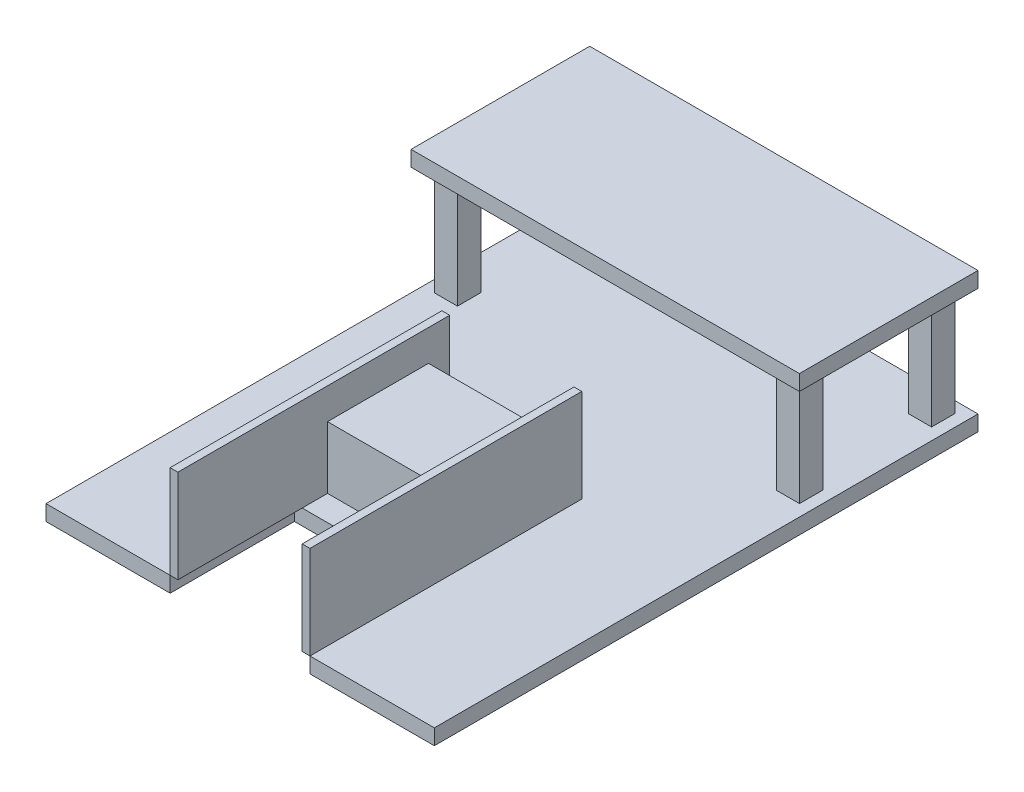
SolidWorks part; units mm, degrees
ref_plane "Front Plane" through (0, 0, 0) normal (0, 0, 1) x (1, 0, 0)
ref_plane "Top Plane" through (0, 0, 0) normal (0, 1, 0) x (1, 0, 0)
ref_plane "Right Plane" through (0, 0, 0) normal (1, 0, 0) x (0, 0, -1)
sketch "Sketch2" plane through (0, 0, 0) normal (0, 1, 0) x (1, 0, 0)
  line L0 (-125, 175) -> (-125, -175)
  line L1 (-125, 175) -> (125, 175)
  line L2 (-125, -175) -> (-45, -175)
  line L3 (125, 175) -> (125, -175)
  line L4 (-125, 175) -> (125, -175) construction
  line L5 (-125, -175) -> (125, 175) construction
  line L6 (0, 192.9969) -> (0, -204.0863) construction
  line L7 (179.2867, 0) -> (-176.6609, 0) construction
  line L8 (-45.0788, -175) -> (-45.0788, -175.07)
  line L9 (-45.0788, -175.07) -> (-45.0788, -95)
  line L10 (-45.0788, -95) -> (44.9212, -95)
  line L11 (44.9652, -175) -> (44.9652, -175.0391)
  line L12 (44.9212, -175) -> (44.9652, -175.0391) construction
  line L13 (-45.0788, -175.07) -> (-45, -175) construction
  line L14 (44.9212, -175) -> (125, -175)
  line L15 (44.9212, -95) -> (44.9212, -175)
  point P1 (0, 0)
  point P11 (0, -135)
  dimension "D1" = 350
  dimension "D2" = 250
  dimension "D3" = 80
  dimension "D4" = 90
  dimension "D5" = 80
  dimension "D6" = 80
extrude "Boss-Extrude1" add sketch "Sketch2" along normal blind 10 contours L10 L15 L14 L3 L1 L0 L2 L9
sketch "Sketch3" plane through (0, 10, 0) normal (0, 1, 0) x (1, 0, 0)
  line L1 (-45.0788, 0) -> (-40.0788, 0)
  line L2 (-45.0788, 0) -> (-45.0788, -175)
  line L3 (-45.0788, -175) -> (-40.0788, -175)
  line L4 (-40.0788, 0) -> (-40.0788, -175)
  line L5 (44.9212, 0) -> (39.9212, 0)
  line L6 (44.9212, 0) -> (44.9212, -175)
  line L7 (44.9212, -175) -> (39.9212, -175)
  line L8 (39.9212, 0) -> (39.9212, -175)
  dimension "D1" = 175
  dimension "D2" = 175
  dimension "D3" = 5
  dimension "D4" = 5
extrude "Boss-Extrude3" add sketch "Sketch3" along normal blind 60 separate body
sketch "Sketch4" plane through (0, 10, 0) normal (0, 1, 0) x (1, 0, 0)
  line L0 (-40.0788, -175) -> (-40.0788, 0) construction
  line L1 (-40.0788, -13.6822) -> (39.9212, -13.6822)
  line L2 (-40.0788, -13.6822) -> (-40.0788, -78.6822)
  line L3 (-40.0788, -78.6822) -> (39.9212, -78.6822)
  line L4 (39.9212, -13.6822) -> (39.9212, -78.6822)
  line L5 (39.9212, 0) -> (39.9212, -175) construction
  line L6 (-157.7293, 160) -> (175.6413, 160) construction
  line L7 (-157.7293, 75) -> (175.6413, 75) construction
  line L8 (-110, 205.2979) -> (-110, 36.6592) construction
  line L9 (110, 205.2979) -> (110, 36.6592) construction
  line L10 (-125, 175) -> (125, 175) construction
  line L11 (-125, 175) -> (-125, -175) construction
  line L12 (125, 175) -> (125, -175) construction
  line L13 (-117.4091, 167.5) -> (-117.4091, 152.5)
  line L14 (-117.4091, 167.5) -> (-102.5909, 167.5)
  line L15 (-117.4091, 152.5) -> (-102.5909, 152.5)
  line L16 (-102.5909, 167.5) -> (-102.5909, 152.5)
  line L17 (-117.4091, 167.5) -> (-102.5909, 152.5) construction
  line L18 (-117.4091, 152.5) -> (-102.5909, 167.5) construction
  line L19 (-117.4667, 82.5306) -> (-117.4667, 67.5306)
  line L20 (-117.4667, 82.5306) -> (-102.6484, 82.5306)
  line L21 (-117.4667, 67.5306) -> (-102.6484, 67.5306)
  line L22 (-102.6484, 82.5306) -> (-102.6484, 67.5306)
  line L23 (-117.4667, 82.5306) -> (-102.6484, 67.5306) construction
  line L24 (-117.4667, 67.5306) -> (-102.6484, 82.5306) construction
  line L25 (102.524, 167.7745) -> (102.524, 152.7745)
  line L26 (102.524, 167.7745) -> (117.3423, 167.7745)
  line L27 (102.524, 152.7745) -> (117.3423, 152.7745)
  line L28 (117.3423, 167.7745) -> (117.3423, 152.7745)
  line L29 (102.524, 167.7745) -> (117.3423, 152.7745) construction
  line L30 (102.524, 152.7745) -> (117.3423, 167.7745) construction
  line L31 (102.7022, 82.5464) -> (102.7022, 67.5464)
  line L32 (102.7022, 82.5464) -> (117.5205, 82.5464)
  line L33 (102.7022, 67.5464) -> (117.5205, 67.5464)
  line L34 (117.5205, 82.5464) -> (117.5205, 67.5464)
  line L35 (102.7022, 82.5464) -> (117.5205, 67.5464) construction
  line L36 (102.7022, 67.5464) -> (117.5205, 82.5464) construction
  point P22 (-110.0576, 75.0306)
  point P23 (-110, 160)
  point P32 (109.9331, 160.2745)
  point P37 (110.1114, 75.0464)
  dimension "D1" = 65
  dimension "D2" = 15
  dimension "D3" = 15
  dimension "D4" = 15
  dimension "D5" = 100
  dimension "D6" = 7.5
extrude "Boss-Extrude4" add sketch "Sketch4" along normal blind 70 separate body
sketch "Sketch5" plane through (0, 80, 0) normal (0, 1, 0) x (1, 0, 0)
  line L0 (39.9212, -78.6822) -> (39.9212, -13.6822) construction
  line L1 (-40.0788, -13.6822) -> (39.9212, -13.6822)
  line L2 (-40.0788, -13.6822) -> (-40.0788, -78.6822)
  line L3 (-40.0788, -78.6822) -> (39.9212, -78.6822)
  line L4 (39.9212, -13.6822) -> (39.9212, -78.6822)
  line L5 (-40.0788, -78.6822) -> (39.9212, -78.6822) construction
extrude "Cut-Extrude1" cut sketch "Sketch5" against normal blind 30
sketch "Sketch6" plane through (0, 80, 0) normal (0, 1, 0) x (1, 0, 0)
  line L0 (125, 175) -> (125, -175) construction
  line L1 (-125, 175) -> (125, 175)
  line L2 (-125, 175) -> (-125, 60.0306)
  line L3 (-125, 60.0306) -> (125, 60.0306)
  line L4 (125, 175) -> (125, 60.0306)
  line L5 (-117.4667, 67.5306) -> (-102.6484, 67.5306) construction
  point P7 (-110.0576, 67.5306)
  dimension "D1" = 7.5
extrude "Boss-Extrude5" add sketch "Sketch6" along normal blind 10
sketch "Sketch7" plane through (0, 0, 0) normal (0, -1, 0) x (1, 0, 0)
  line L1 (-41.9959, 59.7295) -> (47.4842, 59.7295)
  line L2 (-41.9959, 59.7295) -> (-41.9959, -70.2802)
  line L3 (-41.9959, -70.2802) -> (47.4842, -70.2802)
  line L4 (47.4842, 59.7295) -> (47.4842, -70.2802)
extrude "Boss-Extrude6" add sketch "Sketch7" along normal blind 50
sketch "Sketch8" plane through (0, 0, -70.2802) normal (0, 0, -1) x (-1, 0, 0)
  line L0 (41.9959, -50) -> (-47.4842, -50) construction
  line L1 (-41.4842, -6) -> (35.9959, -6)
  line L2 (-41.4842, -6) -> (-41.4842, -44)
  line L3 (-41.4842, -44) -> (35.9959, -44)
  line L4 (35.9959, -6) -> (35.9959, -44)
  line L5 (41.9959, -50) -> (41.9959, 0) construction
  line L6 (-47.4842, -50) -> (-47.4842, 0) construction
  line L7 (41.9959, 0) -> (-47.4842, 0) construction
  dimension "D1" = 6
  dimension "D2" = 6
  dimension "D3" = 6
  dimension "D4" = 6
extrude "Cut-Extrude4" cut sketch "Sketch8" against normal through all
